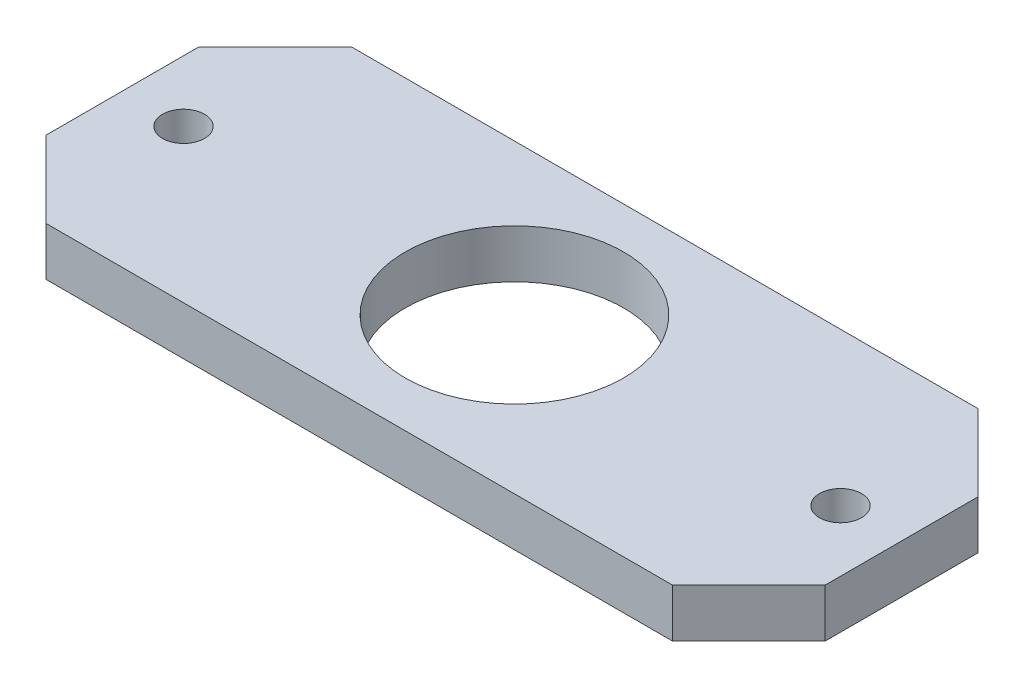
SolidWorks part; units mm, degrees
ref_plane "Front Plane" through (0, 0, 0) normal (0, 0, 1) x (1, 0, 0)
ref_plane "Top Plane" through (0, 0, 0) normal (0, 1, 0) x (1, 0, 0)
ref_plane "Right Plane" through (0, 0, 0) normal (1, 0, 0) x (0, 0, -1)
sketch "Sketch1" plane through (0, 0, 0) normal (0, 1, 0) x (1, 0, 0)
  line L1 (-0.7954, -6.2369) -> (81.2046, -6.2369)
  line L2 (-0.7954, -6.2369) -> (-0.7954, 63.7631)
  line L3 (-0.7954, 63.7631) -> (81.2046, 63.7631)
  line L4 (81.2046, -6.2369) -> (81.2046, 63.7631)
  dimension "D1" = 82
  dimension "D2" = 70
extrude "Boss-Extrude1" add sketch "Sketch1" along normal blind 6.35
sketch "Sketch4" plane through (0, 6.35, 0) normal (0, 1, 0) x (1, 0, 0)
  circle A1 centre (40.245, 29.0407) radius 14.295
  dimension "D1" = 28.59
extrude "Cut-Extrude3" cut sketch "Sketch4" against normal through all
sketch "Sketch7" plane through (-0.7954, 0, 0) normal (-1, 0, 0) x (0, 0, 1)
  line L1 (6.2369, 6.35) -> (-63.7631, 6.35)
  line L2 (6.2369, 6.35) -> (6.2369, 0)
  line L3 (6.2369, 0) -> (-63.7631, 0)
  line L4 (-63.7631, 6.35) -> (-63.7631, 0)
extrude "Boss-Extrude2" add sketch "Sketch7" along normal blind 10
sketch "Sketch8" plane through (81.2046, 0, 0) normal (1, 0, 0) x (0, 0, -1)
  line L1 (-6.2369, 0) -> (63.7631, 0)
  line L2 (-6.2369, 0) -> (-6.2369, 6.35)
  line L3 (-6.2369, 6.35) -> (63.7631, 6.35)
  line L4 (63.7631, 0) -> (63.7631, 6.35)
extrude "Boss-Extrude3" add sketch "Sketch8" along normal blind 10
sketch "Sketch6" plane through (0, 0, 0) normal (0, -1, 0) x (1, 0, 0)
  line L0 (-0.7954, -28.7631) -> (81.2046, -28.7631) construction
  line L1 (-10.7954, -63.7631) -> (-10.7954, 6.2369) construction
  line L2 (91.2046, 6.2369) -> (91.2046, -63.7631) construction
  circle A0 centre (-2.7954, -28.7631) radius 2.75
  circle A1 centre (83.2046, -28.7631) radius 2.75
  dimension "D3" = 5.5
  dimension "D4" = 5.5
  dimension "D1" = 8
  dimension "D2" = 8
extrude "Cut-Extrude4" cut sketch "Sketch6" against normal blind 10
chamfer "Chamfer1" distance 25 angle 45 4 edges at (91.2046, 3.175, 6.2369) (91.2046, 3.175, -63.7631) (-10.7954, 3.175, -63.7631) (-10.7954, 3.175, 6.2369)
sketch "Sketch9" plane through (0, 0, 0) normal (0, -1, 0) x (1, 0, 0)
  line L1 (-14.1959, -8.7631) -> (97.8902, -8.7631)
  line L2 (-14.1959, -8.7631) -> (-14.1959, -48.7631)
  line L3 (-14.1959, -48.7631) -> (97.8902, -48.7631)
  line L4 (97.8902, -8.7631) -> (97.8902, -48.7631)
  circle A0 centre (83.2046, -28.7631) radius 2.75 construction
  dimension "D2" = 20
  dimension "D1" = 20
extrude "Cut-Extrude6" cut sketch "Sketch9" against normal up to next (6.35 mm away) flip side to cut
